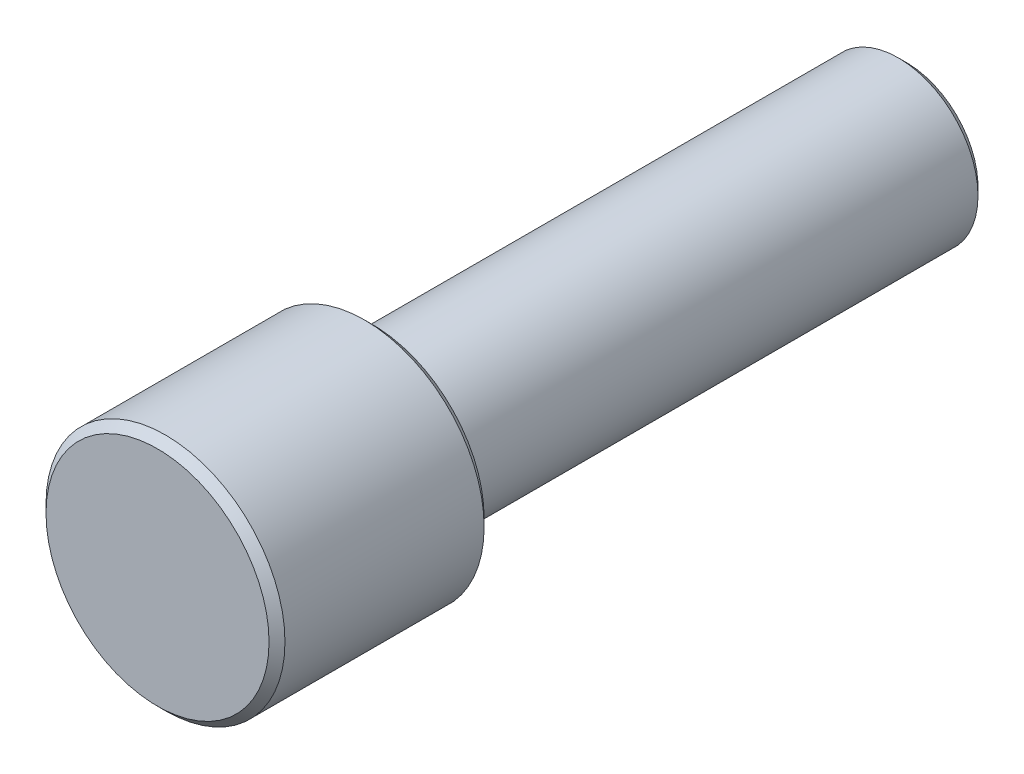
SolidWorks part; units mm, degrees
ref_plane "Plan de face" through (0, 0, 0) normal (0, 0, 1) x (1, 0, 0)
ref_plane "Plan de dessus" through (0, 0, 0) normal (0, 1, 0) x (1, 0, 0)
ref_plane "Plan de droite" through (0, 0, 0) normal (1, 0, 0) x (0, 0, -1)
sketch "Esquisse1" plane through (0, 0, 0) normal (0, 0, 1) x (1, 0, 0)
  circle A0 centre (0, 0) radius 15
  dimension "D1" = 30
extrude "Boss.-Extru.1" add sketch "Esquisse1" along normal blind 27
sketch "Esquisse2" plane through (0, 0, 0) normal (0, 0, -1) x (-1, 0, 0)
  circle A0 centre (0, 0) radius 10
  dimension "D1" = 20
extrude "Boss.-Extru.2" add sketch "Esquisse2" along normal blind 67
chamfer "Chanfrein1" distance 1 angle 45 3 edges at (-10, 0, -67) (15, 0, 0) (15, 0, 27)
fillet "Congé1" radius 1.5 1 edges at (10, 0, 0)
